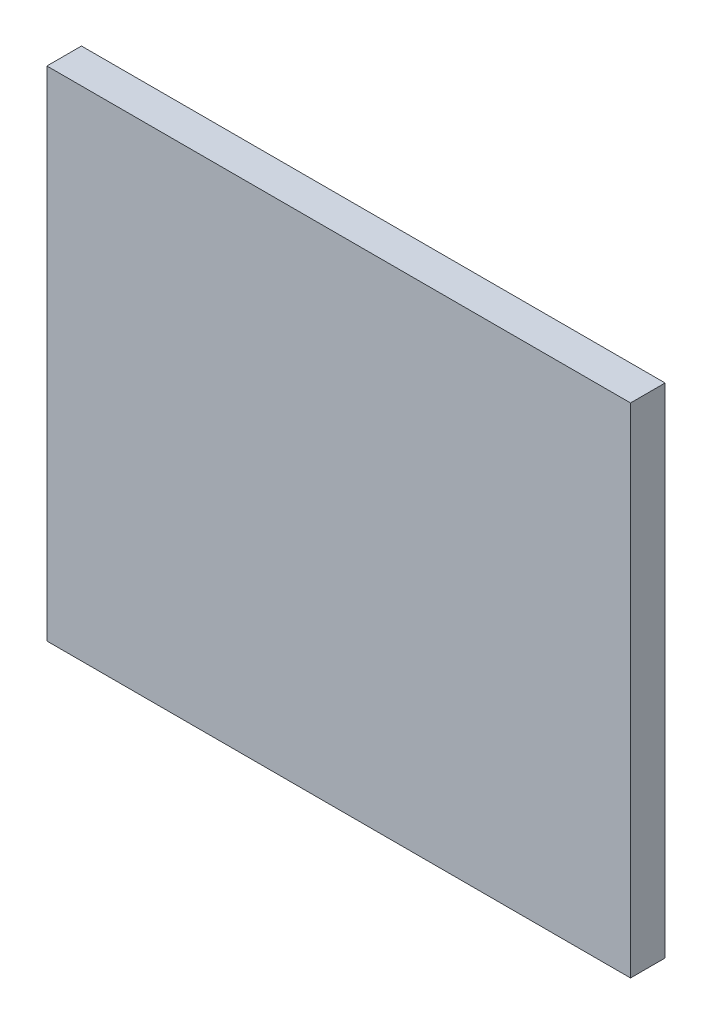
SolidWorks part; units mm, degrees
ref_plane "Front Plane" through (0, 0, 0) normal (0, 0, 1) x (1, 0, 0)
ref_plane "Top Plane" through (0, 0, 0) normal (0, 1, 0) x (1, 0, 0)
ref_plane "Right Plane" through (0, 0, 0) normal (1, 0, 0) x (0, 0, -1)
sketch "Sketch1" plane through (0, 0, 0) normal (0, 0, 1) x (1, 0, 0)
  line L4 (67.5, 95.1988) -> (-67.5, 95.1988)
  line L5 (-67.5, 95.1988) -> (-67.5, -20)
  line L6 (-67.5, -20) -> (67.5, -20)
  line L7 (67.5, -20) -> (67.5, 95.1988)
  line L8 (67.5, 95.1988) -> (-67.5, 95.1988)
  line L9 (-67.5, 95.1988) -> (-67.5, -20)
  line L10 (-67.5, -20) -> (67.5, -20)
  line L11 (67.5, -20) -> (67.5, 95.1988)
  dimension "D1" = 0
extrude "Boss-Extrude1" add sketch "Sketch1" along normal blind 8 from surface at 50
